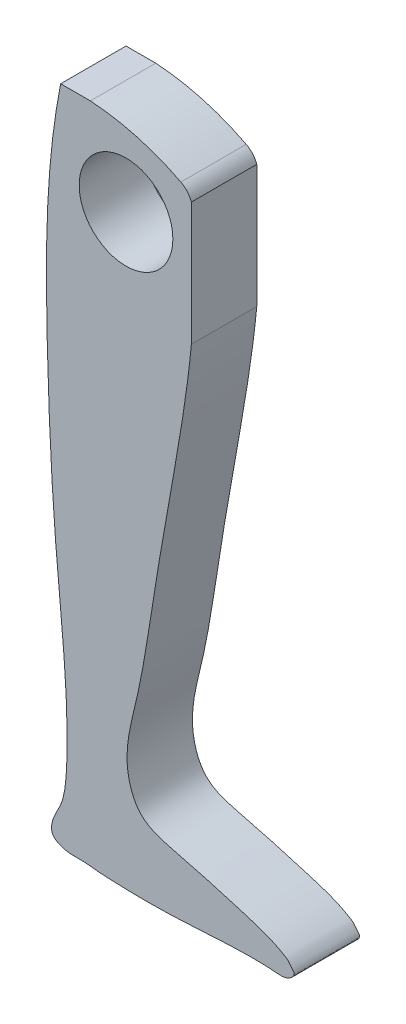
SolidWorks part; units mm, degrees
ref_plane "Front Plane" through (0, 0, 0) normal (0, 0, 1) x (1, 0, 0)
ref_plane "Top Plane" through (0, 0, 0) normal (0, 1, 0) x (1, 0, 0)
ref_plane "Right Plane" through (0, 0, 0) normal (1, 0, 0) x (0, 0, -1)
sketch "Sketch1" plane through (0, 0, 0) normal (0, 0, 1) x (1, 0, 0)
  line L1 (0, 0) -> (6, 0)
  line L3 (0, -30) -> (6, -30)
  line L4 (6, 0) -> (6, -30)
  circle A0 centre (3, -3.6) radius 2.15
  arc A1 (5.5162, -1.1496) -> (0, 0) centre (0.682, -10.5372) ccw
  arc A2 (5.5162, -1.1496) -> (6.0544, -1.9486) centre (5.0584, -2.0386) cw
  spline S0 degree 3 poles (0, 0) (-0.6911, -3.4731) (-0.707, -9.7972) (-0.3074, -18.6561) (0.3875, -24.2948) (0.2544, -27.5583) (0.1214, -28.5796) (-0.3794, -29.3088) (-0.4716, -30.0262) (0.242, -30.464) (0.9315, -30.3472) (1.6321, -30.4503) (2.821, -30.5153) (5.3554, -30.5708) (7.9148, -30.2924) (9.8162, -30.3616) (10.3748, -30.4439) (10.8031, -30.0516) (10.5785, -29.8095) (10.4581, -29.6305) (9.742, -29.1752) (8.0306, -28.6416) (5.8763, -28.019) (3.6349, -27.5205) (2.7741, -25.3369) (3.6755, -22.3209) (4.2586, -18.0945) (5.1892, -12.9608) (6.1175, -7.5442) (6.2186, -3.7671) (6.0544, -1.9486) knots 0 0 0 0 0.140411 0.250882 0.354066 0.364891 0.3817 0.393575 0.400647 0.40682 0.423094 0.427756 0.434983 0.470514 0.528627 0.53731 0.546082 0.551292 0.55392 0.55766 0.560136 0.587167 0.628172 0.6528 0.671012 0.713582 0.774573 0.842137 0.921181 0.992983 0.992983 0.992983 0.992983
  dimension "D3" = 4.3
  dimension "D4" = 3
  dimension "D6" = 1
  dimension "D1" = 6
  dimension "D2" = 30
  dimension "D5" = 3.6
extrude "Boss-Extrude1" add sketch "Sketch1" along normal blind 3
